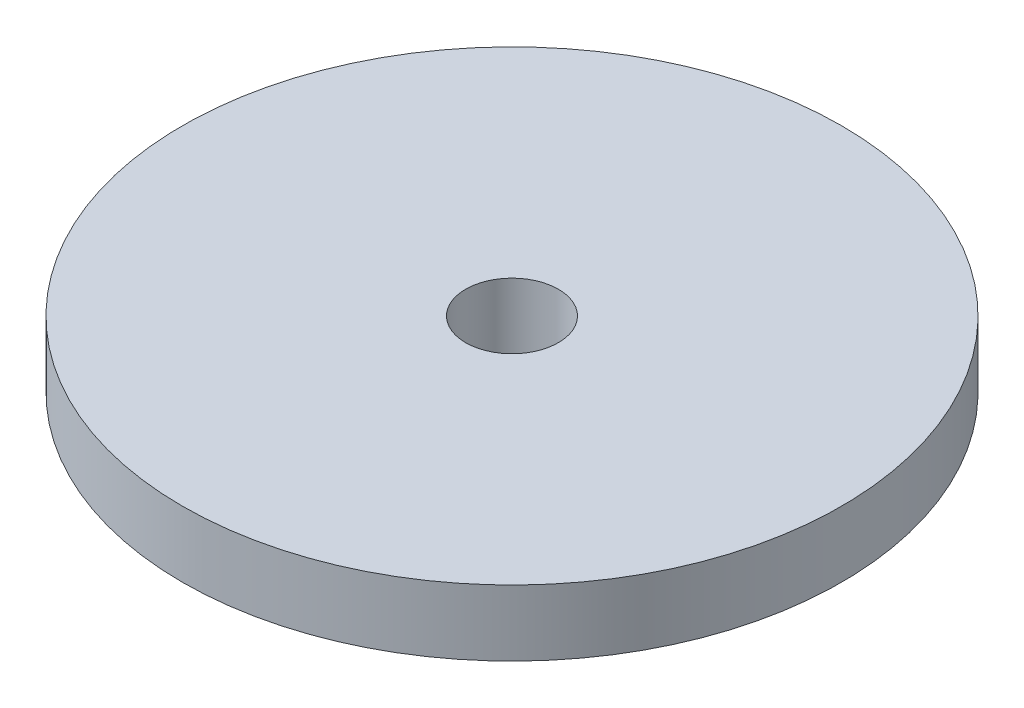
SolidWorks part; units mm, degrees
material "ABS"
ref_plane "Front Plane" through (0, 0, 0) normal (0, 0, 1) x (1, 0, 0)
ref_plane "Top Plane" through (0, 0, 0) normal (0, 1, 0) x (1, 0, 0)
ref_plane "Right Plane" through (0, 0, 0) normal (1, 0, 0) x (0, 0, -1)
sketch "Sketch1" plane through (0, 0, 0) normal (0, 1, 0) x (1, 0, 0)
  circle A0 centre (0, 0) radius 12.7
  circle A1 centre (0, 0) radius 1.7859
  dimension "D1" = 25.4
  dimension "D2" = 3.5719
extrude "Boss-Extrude1" add sketch "Sketch1" along normal blind 2.54
